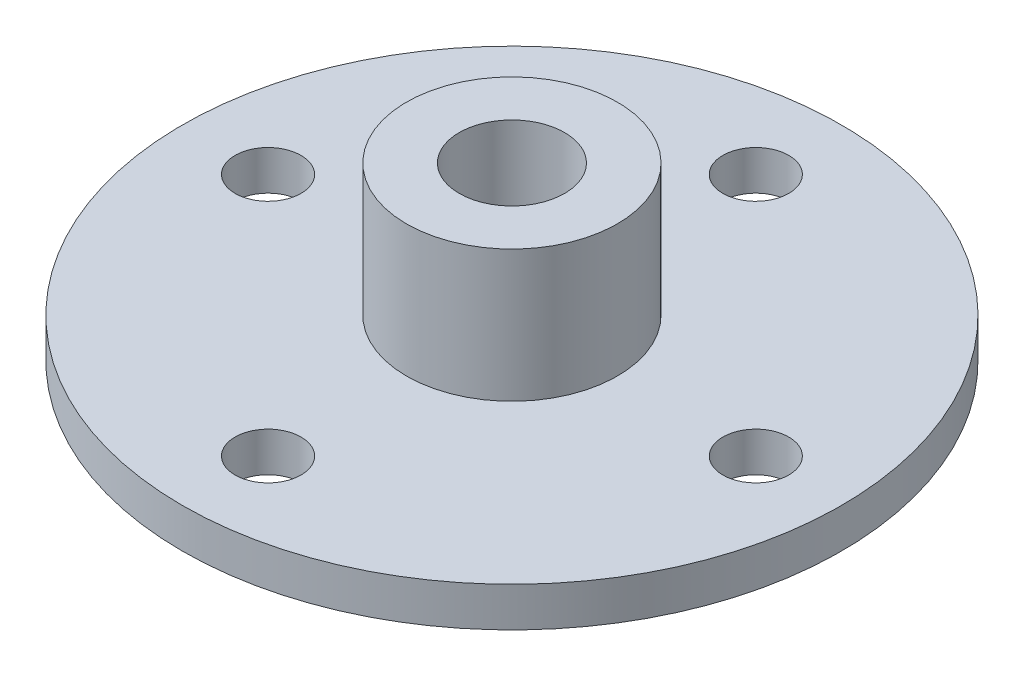
SolidWorks part; units mm, degrees
ref_plane "Front Plane" through (0, 0, 0) normal (0, 0, 1) x (1, 0, 0)
ref_plane "Top Plane" through (0, 0, 0) normal (0, 1, 0) x (1, 0, 0)
ref_plane "Right Plane" through (0, 0, 0) normal (1, 0, 0) x (0, 0, -1)
sketch "Sketch2" plane through (0, 0, 0) normal (0, 1, 0) x (1, 0, 0)
  line L0 (0, 0) -> (-18.5, 0)
  circle A0 centre (-18.5, 0) radius 2.5
  circle A1 centre (0, 0) radius 25
  circle A2 centre (0, 18.5) radius 2.5
  circle A3 centre (18.5, 0) radius 2.5
  circle A4 centre (0, -18.5) radius 2.5
  dimension "D1" = 4
extrude "Boss-Extrude1" add sketch "Sketch2" along normal blind 3
sketch "Sketch3" plane through (0, 3, 0) normal (0, 1, 0) x (1, 0, 0)
  circle A0 centre (0, 0) radius 4
  circle A1 centre (0, 0) radius 8
extrude "Boss-Extrude2" add sketch "Sketch3" along normal blind 10
